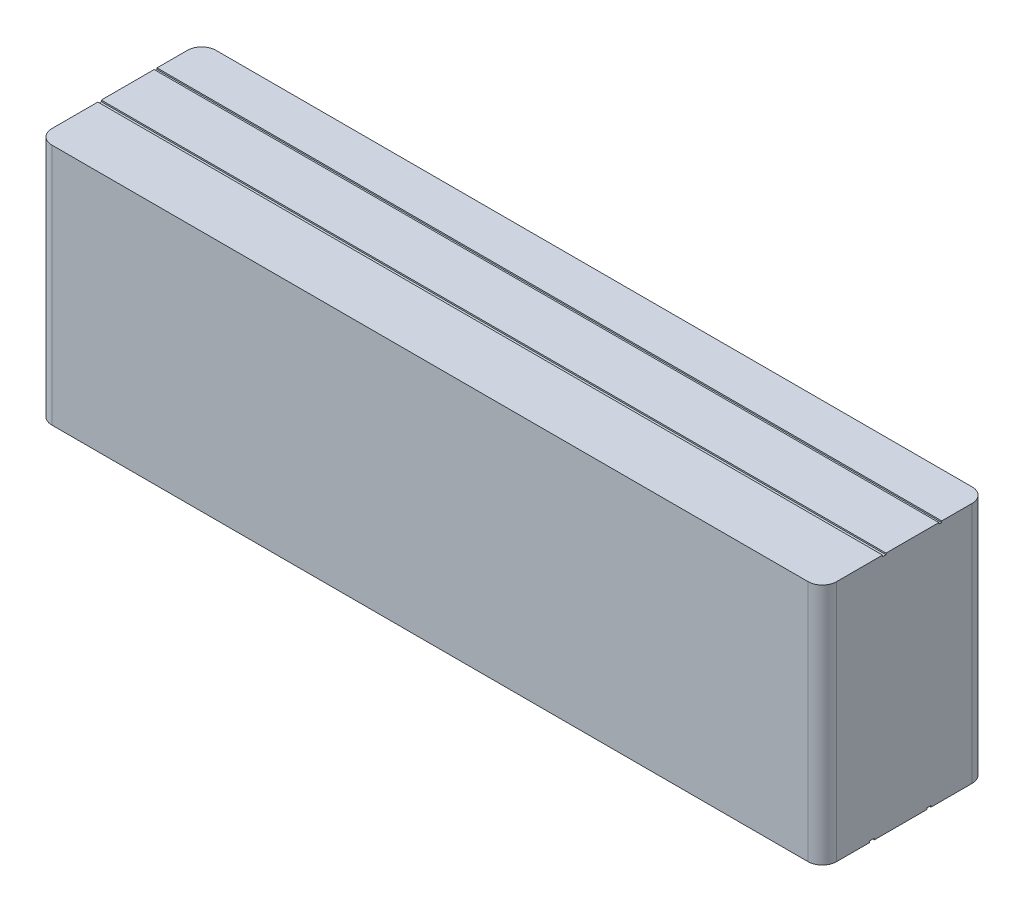
SolidWorks part; units mm, degrees
ref_plane "Front Plane" through (0, 0, 0) normal (0, 0, 1) x (1, 0, 0)
ref_plane "Top Plane" through (0, 0, 0) normal (0, 1, 0) x (1, 0, 0)
ref_plane "Right Plane" through (0, 0, 0) normal (1, 0, 0) x (0, 0, -1)
sketch "Sketch1" plane through (0, 0, 0) normal (0, 0, 1) x (1, 0, 0)
  line L1 (0, 0) -> (-110, 0)
  line L2 (0, 0) -> (0, 34)
  line L3 (0, 34) -> (-110, 34)
  line L4 (-110, 0) -> (-110, 34)
  dimension "D1" = 110
  dimension "D2" = 34
extrude "Boss-Extrude1" add sketch "Sketch1" along normal blind 23
sketch "Sketch2" plane through (0, 0, 0) normal (0, -1, 0) x (1, 0, 0)
  line L1 (-113.1007, 16.3718) -> (0.854, 16.3718)
  line L2 (-113.1007, 16.3718) -> (-113.1007, 15.7061)
  line L3 (-113.1007, 15.7061) -> (0.854, 15.7061)
  line L4 (0.854, 16.3718) -> (0.854, 15.7061)
  line L5 (-113.1007, 8.3398) -> (2.1425, 8.3398)
  line L6 (-113.1007, 8.3398) -> (-113.1007, 7.7761)
  line L7 (-113.1007, 7.7761) -> (2.1425, 7.7761)
  line L8 (2.1425, 8.3398) -> (2.1425, 7.7761)
extrude "Cut-Extrude1" cut sketch "Sketch2" against normal blind 0.2
sketch "Sketch3" plane through (0, 34, 0) normal (0, 1, 0) x (1, 0, 0)
  line L1 (2.453, -6.2605) -> (-112.7097, -6.2605)
  line L2 (2.453, -6.2605) -> (2.453, -6.6631)
  line L3 (2.453, -6.6631) -> (-112.7097, -6.6631)
  line L4 (-112.7097, -6.2605) -> (-112.7097, -6.6631)
  line L5 (2.453, -14.5554) -> (-112.7097, -14.5554)
  line L6 (2.453, -14.5554) -> (2.453, -14.0722)
  line L7 (2.453, -14.0722) -> (-112.7097, -14.0722)
  line L8 (-112.7097, -14.5554) -> (-112.7097, -14.0722)
extrude "Cut-Extrude2" cut sketch "Sketch3" against normal blind 0.2
fillet "Fillet1" radius 2 1 edges at (0, 17, 0)
fillet "Fillet2" radius 2 1 edges at (0, 17, 23)
fillet "Fillet3" radius 2 1 edges at (-110, 17, 0)
fillet "Fillet4" radius 2 1 edges at (-110, 17, 23)
sketch "Sketch4" plane through (0, 0, 0) normal (0, 0, -1) x (-1, 0, 0)
  text T0 "2200 Mah 3S" font "Century Gothic" height 3.5
extrude "Cut-Extrude3" cut sketch "Sketch4" against normal blind 0.2
sketch "Sketch5" plane through (0, 0, 0) normal (0, 0, -1) x (-1, 0, 0)
  line L0 (2, 7.8039) -> (83.032, 11.9761)
  line L1 (2, 34) -> (2, 0) construction
  line L2 (83.032, 11.9761) -> (108, 23.2314)
  line L3 (108, 0) -> (108, 34) construction
  line L4 (108, 23.2314) -> (108, 0)
  line L5 (108, 0) -> (2, 0)
  line L6 (2, 0) -> (2, 7.8039)
extrude "Cut-Extrude4" cut sketch "Sketch5" against normal blind 0.05
